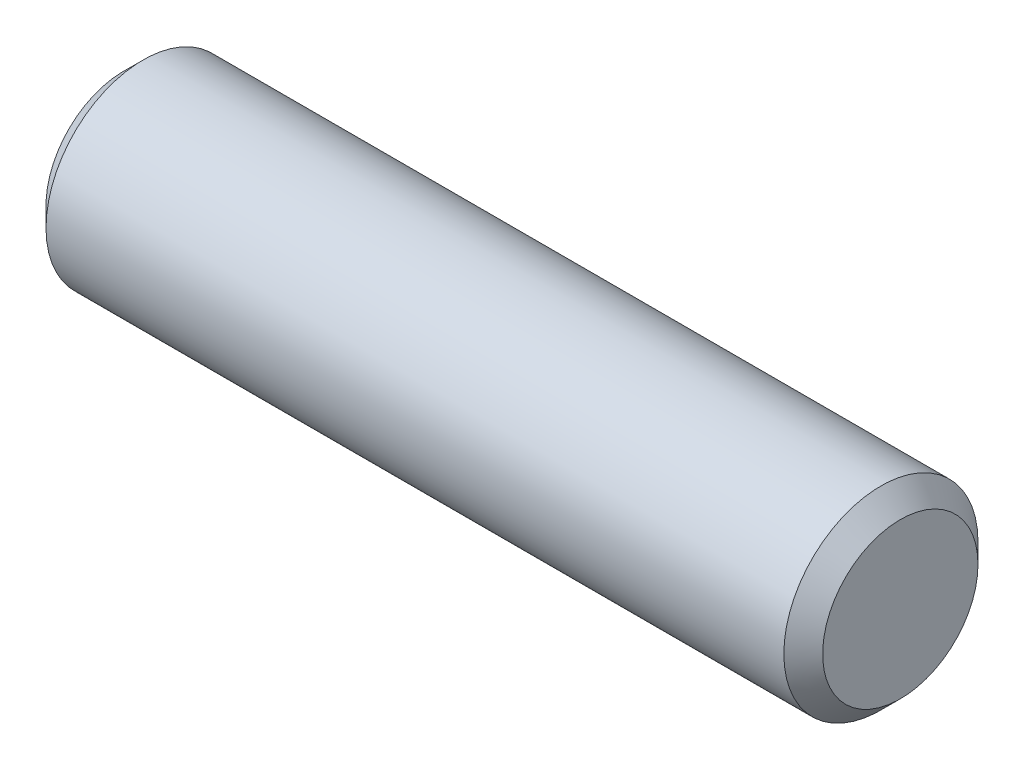
SolidWorks part; units mm, degrees
ref_plane "Front Plane" through (0, 0, 0) normal (0, 0, 1) x (1, 0, 0)
ref_plane "Top Plane" through (0, 0, 0) normal (0, 1, 0) x (1, 0, 0)
ref_plane "Right Plane" through (0, 0, 0) normal (1, 0, 0) x (0, 0, -1)
sketch "Sketch1" plane through (0, 0, 0) normal (0, 0, 1) x (1, 0, 0)
  line L0 (-12.7, 0) -> (12.7, 0) construction
  line L1 (-12.7, 3.175) -> (-12.7, -3.175) construction
  line L2 (12.7, 3.175) -> (12.7, -3.175) construction
  dimension "Diameter" = 6.35
  dimension "Length" = 25.4
sketch "Sketch2" plane through (0, 0, 0) normal (1, 0, 0) x (0, 0, -1)
  circle A0 centre (0, 0) radius 3.175
extrude "Extrude1" add sketch "Sketch2" against normal up to vertex (12.7 mm away) and the other way up to vertex (12.7 mm away) up to point (-12.7, 0, 0) other way up to point (12.7, 0, 0)
chamfer "Chamfer1" distance 0.635 angle 45 2 edges at (12.7, 0, -3.175) (-12.7, 0, -3.175)
equation "\"D1@Chamfer1\" = \"Diameter@Sketch1\"*.1"
